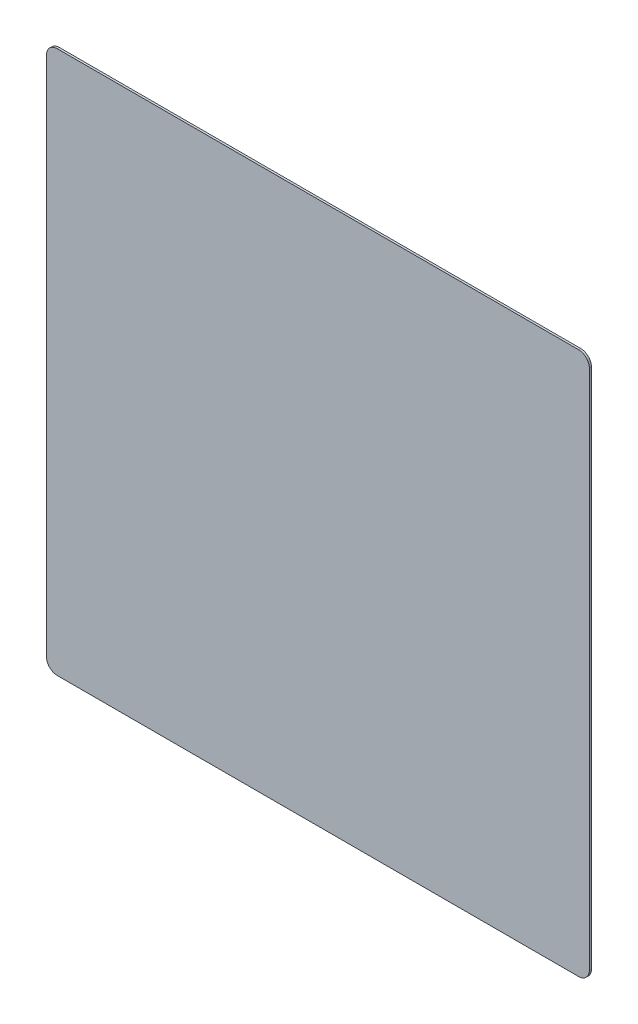
SolidWorks part; units mm, degrees
material "Acrylic (Medium-high impact)"
ref_plane "Front Plane" through (0, 0, 0) normal (0, 0, 1) x (1, 0, 0)
ref_plane "Top Plane" through (0, 0, 0) normal (0, 1, 0) x (1, 0, 0)
ref_plane "Right Plane" through (0, 0, 0) normal (1, 0, 0) x (0, 0, -1)
sketch "Sketch1" plane through (0, 0, 0) normal (0, 0, 1) x (1, 0, 0)
  line L1 (-505, 505) -> (505, 505)
  line L2 (-505, 505) -> (-505, -505)
  line L3 (-505, -505) -> (505, -505)
  line L4 (505, 505) -> (505, -505)
  line L5 (-505, 505) -> (505, -505) construction
  line L6 (-505, -505) -> (505, 505) construction
  dimension "D1" = 1010
extrude "Boss-Extrude1" add sketch "Sketch1" along normal blind 4
fillet "Fillet1" radius 20 4 edges at (505, -505, 2) (-505, -505, 2) (-505, 505, 2) (505, 505, 2)
